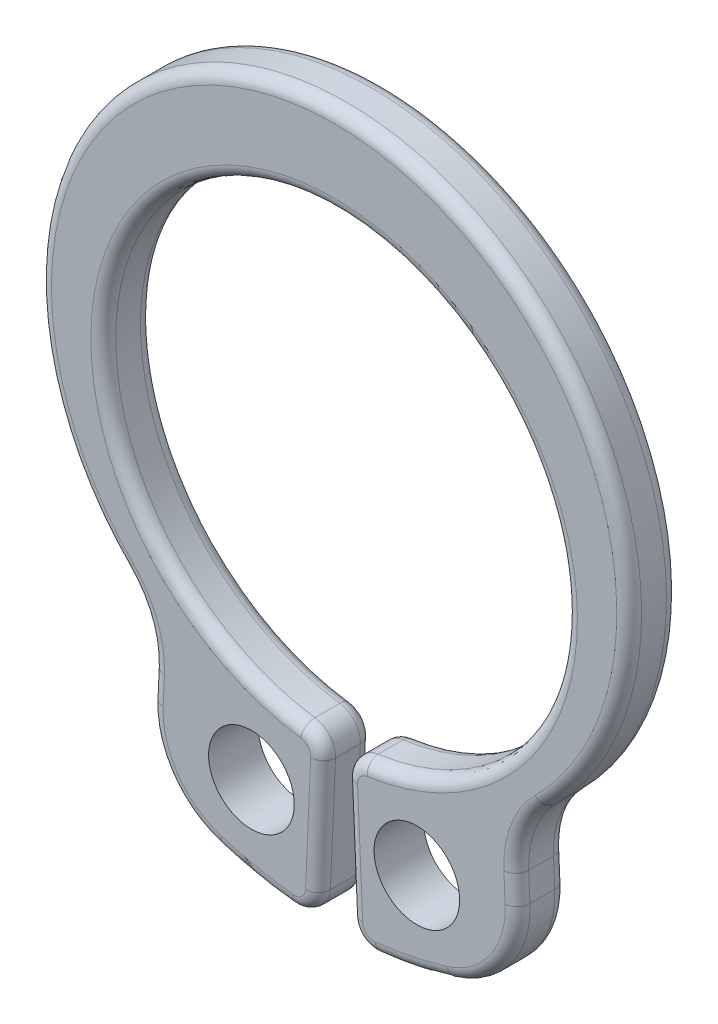
SolidWorks part; units mm, degrees
ref_plane "Front" through (0, 0, 0) normal (0, 0, 1) x (1, 0, 0)
ref_plane "Top" through (0, 0, 0) normal (0, 1, 0) x (1, 0, 0)
ref_plane "Right" through (0, 0, 0) normal (1, 0, 0) x (0, 0, -1)
sketch "Sketch1" plane through (0, 0, 0) normal (0, 0, 1) x (1, 0, 0)
  line L0 (0, 0) -> (-4.027, -2.325) construction
  line L1 (0, 7.95) -> (0, -7.95) construction
  line L2 (-3.7543, -7.0163) -> (-3.6271, -4.2008) construction
  line L3 (0, 0) -> (4.027, -2.325) construction
  line L4 (-3.6271, -4.2008) -> (-4.2153, -4.882) construction
  line L5 (-3.6271, -4.2008) -> (0, 0) construction
  line L6 (0, 4.65) -> (0, 6.45) construction
  line L7 (0, 6.45) -> (0, 5.55) construction
  line L8 (0, -4.65) -> (0, -7.95) construction
  line L9 (-2.1032, -7.6746) -> (0, 0) construction
  line L10 (0, 0) -> (-0.3471, -7.95) construction
  line L11 (-3.7543, -7.0163) -> (0, 0) construction
  line L12 (-3.6628, -4.9899) -> (-4.2195, -3.6781) construction
  line L13 (-3.9411, -4.334) -> (-3.6271, -4.2008) construction
  line L14 (-1.229, -4.4847) -> (-2.1032, -7.6746) construction
  line L15 (-1.6661, -6.0796) -> (-0.9428, -6.2779) construction
  arc A0 (0, 6.45) -> (-3.6271, -4.2008) centre (0, 0.507) ccw construction
  circle A2 centre (0, 0) radius 6.45 construction
  arc A3 (-3.7543, -7.0163) -> (-0.3471, -7.95) centre (0, 0) ccw construction
  circle A4 centre (0, 0) radius 4.65 construction
  circle A6 centre (-1.6661, -6.0796) radius 0.75 construction
  arc A7 (-4.2195, -3.6781) -> (-3.6628, -4.9899) centre (-5.5834, -5.0309) cw construction
  point P5 (-4.027, -2.325)
  point P11 (4.027, -2.325)
  point P24 (-3.043, -5.687)
  point P35 (0, 6.45)
  point P36 (0, 4.65)
  point P37 (0, -4.65)
  point P38 (0, -7.95)
  dimension "Ring ID" = 9.3
  dimension "Hole Diameter" = 1.5
  dimension "D10" = 1.921
  dimension "Max Sec." = 1.8
  dimension "Lug Height" = 3.3
  dimension "D6" = 2.5
  dimension "D5" = 2.8184
  dimension "D8" = 1.425
  dimension "D3" = 120
  dimension "D7" = 60
  dimension "D2" = 3.5625
  dimension "D4" = 1.425
sketch "Sketch5" plane through (0, 0, 0) normal (0, 1, 0) x (1, 0, 0)
  line L0 (-6.45, 0.5) -> (-6.45, -0.5) construction
  line L2 (0, 0.5) -> (0, -0.5) construction
  line L4 (-6.45, 0) -> (6.45, 0) construction
  point P3 (-6.45, 0)
  point P6 (0, 0)
  dimension "Ring Thickness" = 1
sketch "Sketch2" plane through (0, 0, 0) normal (0, 0, 1) x (1, 0, 0)
  line L0 (-3.7543, -7.0163) -> (-3.6271, -4.2008) construction
  line L1 (-3.7543, -7.0163) -> (-3.6271, -4.2008)
  line L2 (0, 6.45) -> (0, 4.65)
  line L3 (-0.3471, -7.95) -> (-0.2028, -4.6456)
  line L4 (0, 0) -> (-0.3471, -7.95) construction
  arc A0 (0, 6.45) -> (-3.6271, -4.2008) centre (0, 0.507) ccw construction
  arc A1 (-3.7543, -7.0163) -> (-0.3471, -7.95) centre (0, 0) ccw construction
  circle A2 centre (-1.6661, -6.0796) radius 0.75 construction
  circle A3 centre (-1.6661, -6.0796) radius 0.8625
  arc A4 (0, 6.45) -> (-3.6271, -4.2008) centre (0, 0.507) ccw
  arc A5 (-3.7543, -7.0163) -> (-0.3471, -7.95) centre (0, 0) ccw
  circle A6 centre (-1.6661, -6.0796) radius 0.75 construction
  circle A7 centre (0, 0) radius 4.65 construction
  arc A8 (0, 4.65) -> (-0.2028, -4.6456) centre (0, 0) ccw
  dimension "D1" = 1.725
extrude "Boss-Extrude1" add sketch "Sketch2" along normal mid plane 1
fillet "Fillet1" radius 1.921 2 edges at (-3.6271, -4.2008, 0) (-3.7543, -7.0163, 0)
fillet "Fillet2" radius 0.4803 2 edges at (-0.3471, -7.95, 0) (-0.2028, -4.6456, 0)
mirror "Mirror1" about plane through (0, 6.45, 0.5) normal (-1, 0, 0) of bodies 109
fillet "Fillet3" radius 0.25 32 edges at (-0.3337, -4.7744, -0.5) (-0.2741, -6.2788, -0.5) (-0.4924, -7.7982, -0.5) (-1.6057, -7.7939, -0.5) (-3.3456, -6.8758, -0.5) (-3.6812, -5.3983, -0.5) (-3.7948, -4.3362, -0.5) (0, 6.45, -0.5) (3.7948, -4.3362, 0.5) (3.7948, -4.3362, -0.5) (3.6812, -5.3983, -0.5) (3.6812, -5.3983, 0.5) (3.3456, -6.8758, 0.5) (3.3456, -6.8758, -0.5) (1.6057, -7.7939, -0.5) (1.6057, -7.7939, 0.5) (0.4924, -7.7982, 0.5) (0.4924, -7.7982, -0.5) (0.2741, -6.2788, 0.5) (0.2741, -6.2788, -0.5) (0.3337, -4.7744, 0.5) (0.3337, -4.7744, -0.5) (-0.3337, -4.7744, 0.5) (-0.2741, -6.2788, 0.5) (-0.4924, -7.7982, 0.5) (-1.6057, -7.7939, 0.5) (-3.3456, -6.8758, 0.5) (-3.6812, -5.3983, 0.5) (-3.7948, -4.3362, 0.5) (0, 6.45, 0.5) (0, 4.65, -0.5) (0, 4.65, 0.5)
sketch "Sketch3" plane through (0, 0, 0.5) normal (0, 0, 1) x (1, 0, 0)
  line L0 (3.5474, -3.0064) -> (4.2225, -3.675) construction
  line L1 (4.2225, -3.675) -> (4.8912, -2.9999) construction
  line L2 (0, 6.45) -> (0, 4.65) construction
  circle A0 centre (0, 0) radius 4.65 construction
  arc A1 (-4.2225, -3.675) -> (4.2225, -3.675) centre (0, 0.507) ccw construction
equation "\"Thickness@Boss-Extrude1\"=\"Ring Thickness@Sketch5\""
equation "\"D2@Sketch1\"=\"Hole Diameter@Sketch1\"*2.375"
equation "\"D4@Sketch1\"=\"D2@Sketch1\"/2.5"
equation "\"D8@Sketch1\"=\"D4@Sketch1\""
equation "\"D1@Sketch2\"=\"Hole Diameter@Sketch1\"*1.15"
equation "\"D1@Fillet2\"=\"D10@Sketch1\" / 4"
equation "\"D1@Fillet3\"=\"Ring Thickness@Sketch5\"/4"
equation "\"D1@Fillet1\"=\"D10@Sketch1\""
